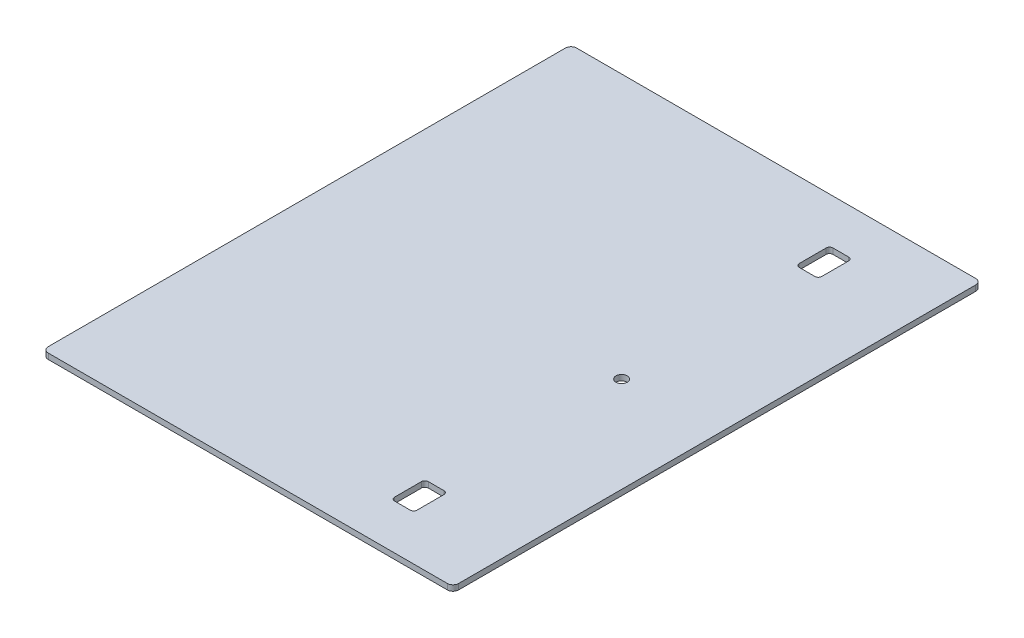
SolidWorks part; units mm, degrees
ref_plane "Front Plane" through (0, 0, 0) normal (0, 0, 1) x (1, 0, 0)
ref_plane "Top Plane" through (0, 0, 0) normal (0, 1, 0) x (1, 0, 0)
ref_plane "Right Plane" through (0, 0, 0) normal (1, 0, 0) x (0, 0, -1)
sketch "Sketch1" plane through (0, 0, 0) normal (0, 1, 0) x (1, 0, 0)
  line L1 (-115.8875, -149.225) -> (115.8875, -149.225)
  line L2 (-115.8875, -149.225) -> (-115.8875, 149.225)
  line L3 (-115.8875, 149.225) -> (115.8875, 149.225)
  line L4 (115.8875, -149.225) -> (115.8875, 149.225)
  line L5 (-115.8875, -149.225) -> (115.8875, 149.225) construction
  line L6 (-115.8875, 149.225) -> (115.8875, -149.225) construction
  point P0 (0, 0)
  dimension "D1" = 298.45
  dimension "D2" = 231.775
extrude "Boss-Extrude1" add sketch "Sketch1" along normal blind 3.175
hole_wizard "1/4 (0.25) Diameter Hole1" positions "Sketch2" profile "Sketch3" hole size "1/4" standard "ANSI Inch" end condition through all
sketch "Sketch2" plane through (0, 3.175, 0) normal (0, 1, 0) x (1, 0, 0)
  line L0 (115.8875, -149.225) -> (115.8875, 149.225) construction
  point P12 (61.9125, 0)
  dimension "D5" = 53.975
sketch "Sketch3" plane through (61.9125, 3.175, 0) normal (1, 0, 0) x (0, 0, 1)
  line L0 (0, 0) -> (0, 3.175)
  line L1 (0, 3.175) -> (3.175, 3.175)
  line L2 (3.175, 3.175) -> (3.175, 0)
  line L5 (3.175, 0) -> (0, 0)
  line L11 (0, -6.35) -> (0, 107.95) construction
  dimension "Thru Hole Dia." = 6.35
  dimension "Thru Hole Depth" = 3.175
fillet "Fillet1" radius 3.175 4 edges at (-115.8875, 1.5875, 149.225) (115.8875, 1.5875, 149.225) (-115.8875, 1.5875, -149.225) (115.8875, 1.5875, -149.225)
sketch "Sketch4" plane through (0, 3.175, 0) normal (0, 1, 0) x (1, 0, 0)
  line L0 (-112.7125, -149.225) -> (112.7125, -149.225) construction
  line L1 (55.5625, -104.775) -> (68.2625, -104.775)
  line L2 (55.5625, -104.775) -> (55.5625, -123.825)
  line L3 (55.5625, -123.825) -> (68.2625, -123.825)
  line L4 (68.2625, -104.775) -> (68.2625, -123.825)
  line L5 (55.5625, 123.825) -> (68.2625, 123.825)
  line L6 (55.5625, 123.825) -> (55.5625, 104.775)
  line L7 (55.5625, 104.775) -> (68.2625, 104.775)
  line L8 (68.2625, 123.825) -> (68.2625, 104.775)
  line L9 (112.7125, 149.225) -> (-112.7125, 149.225) construction
  line L10 (115.8875, -146.05) -> (115.8875, 146.05) construction
  point P14 (61.9125, -123.825)
  dimension "D1" = 25.4
  dimension "D2" = 25.4
  dimension "D3" = 12.7
  dimension "D4" = 19.05
  dimension "D5" = 53.975
extrude "Cut-Extrude1" cut sketch "Sketch4" against normal through all
fillet "Fillet2" radius 1.905 8 edges at (68.2625, 1.5875, 123.825) (68.2625, 1.5875, 104.775) (55.5625, 1.5875, 104.775) (55.5625, 1.5875, 123.825) (55.5625, 1.5875, -104.775) (68.2625, 1.5875, -104.775) (68.2625, 1.5875, -123.825) (55.5625, 1.5875, -123.825)
